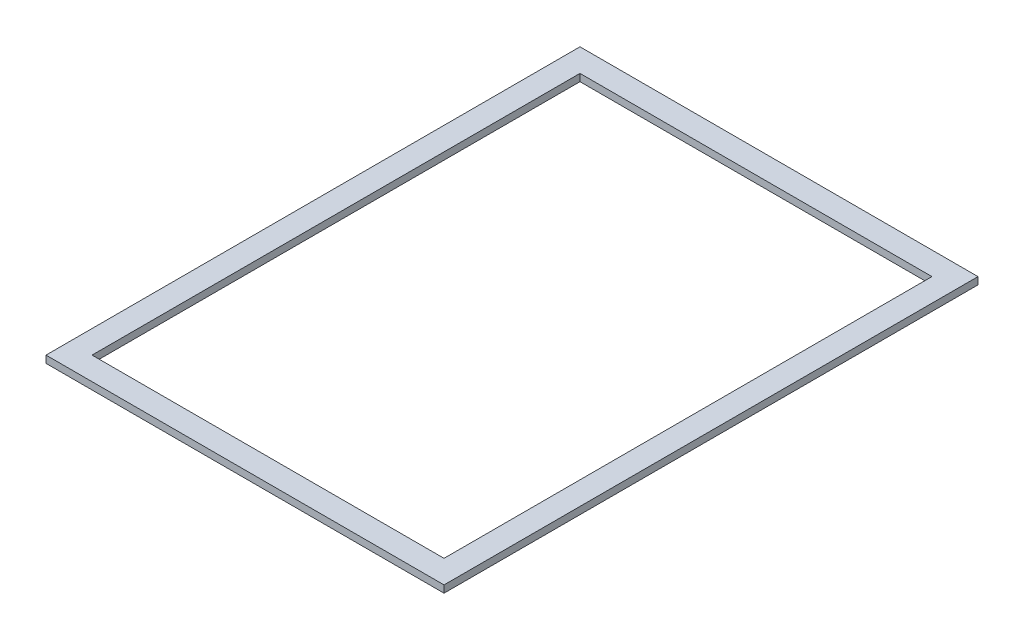
SolidWorks part; units mm, degrees
material "POLYURETHANE (11671)"
ref_plane "Front Plane" through (0, 0, 0) normal (0, 0, 1) x (1, 0, 0)
ref_plane "Top Plane" through (0, 0, 0) normal (0, 1, 0) x (1, 0, 0)
ref_plane "Right Plane" through (0, 0, 0) normal (1, 0, 0) x (0, 0, -1)
sketch "Sketch1" plane through (0, 129.032, 0) normal (0, 1, 0) x (1, 0, 0)
  line L0 (5.08, 112.748) -> (5.08, 5.08)
  line L1 (0, 117.828) -> (87.828, 117.828)
  line L2 (0, 117.828) -> (0, 0)
  line L3 (0, 0) -> (87.828, 0)
  line L4 (87.828, 117.828) -> (87.828, 0)
  line L5 (5.08, 5.08) -> (82.748, 5.08)
  line L6 (82.748, 112.748) -> (82.748, 5.08)
  line L7 (5.08, 112.748) -> (82.748, 112.748)
  dimension "D1" = 5.08
extrude "Boss-Extrude1" add sketch "Sketch1" along normal blind 1.5875
